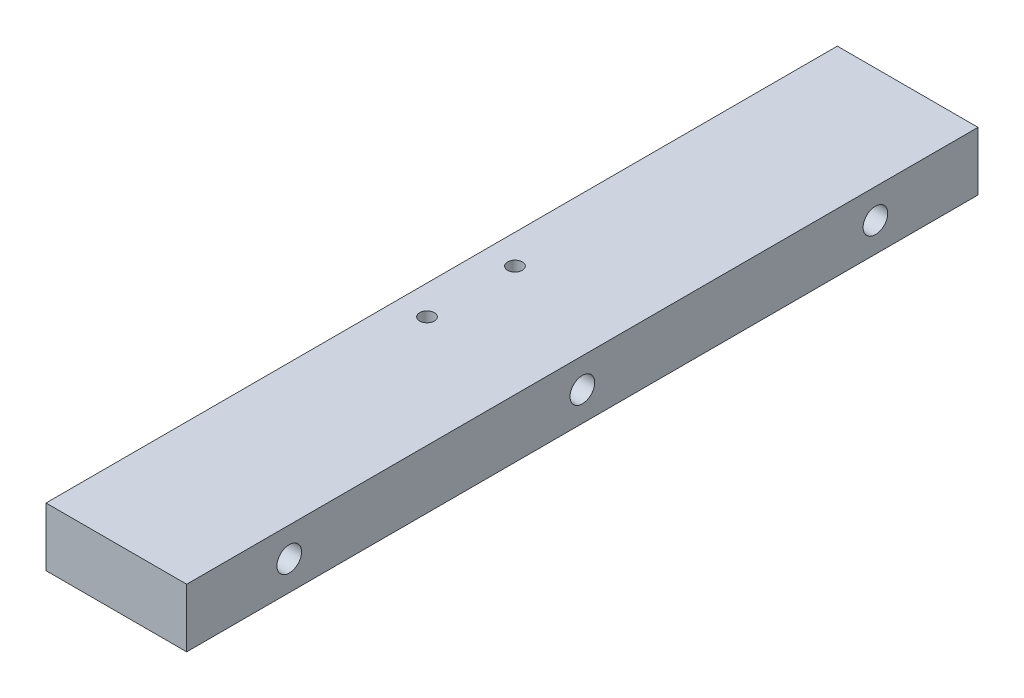
SolidWorks part; units mm, degrees
ref_plane "Front" through (0, 0, 0) normal (0, 0, 1) x (1, 0, 0)
ref_plane "Top" through (0, 0, 0) normal (0, 1, 0) x (1, 0, 0)
ref_plane "Right" through (0, 0, 0) normal (1, 0, 0) x (0, 0, -1)
sketch "Sketch1" plane through (0, 0, 0) normal (0, 1, 0) x (1, 0, 0)
  line L0 (-17.0145, 0) -> (36.7908, 0) construction
  line L1 (0, -67.5) -> (24, -67.5)
  line L2 (0, -67.5) -> (0, 67.5)
  line L3 (0, 67.5) -> (24, 67.5)
  line L4 (24, -67.5) -> (24, 67.5)
  dimension "D1" = 135
  dimension "D2" = 24
extrude "Boss-Extrude1" add sketch "Sketch1" along normal blind 10
hole_wizard "M5x0.8 Tapped Hole1" positions "Sketch3" profile "Sketch2" tap size "M5x0.8" standard "JIS"
sketch "Sketch3" plane through (24, 0, 0) normal (1, 0, 0) x (0, 0, -1)
  line L0 (0, 19.7084) -> (0, -9.2288) construction
  line L2 (-67.5, 0) -> (67.5, 0) construction
  point P0 (0, 5)
  point P1 (-50, 5)
  point P3 (50, 5)
  dimension "D1" = 100
  dimension "D2" = 5
sketch "Sketch2" plane through (24, 5, 0) normal (0, 1, 0) x (0, 0, -1)
  line L0 (0, 0) -> (0, 13.6618)
  line L1 (0, 13.6618) -> (2.1, 12.4)
  line L2 (2.1, 12.4) -> (2.1, 0)
  line L5 (2.1, 0) -> (0, 0)
  line L10 (0, 13.6618) -> (-2.1, 12.4) construction
  line L11 (0, -6.35) -> (0, 107.95) construction
  dimension "Tap Drill Dia." = 4.2
  dimension "Tap Drill Depth" = 12.4
  dimension "Drill Angle" = 118
cosmetic thread "Hole Thread1" parameters "D1"=10, "D2"=5
cosmetic thread "Hole Thread2" parameters "D1"=10, "D2"=5
cosmetic thread "Hole Thread3" parameters "D1"=10, "D2"=5
cosmetic thread "Hole Thread5" parameters "D1"=10, "D2"=5
hole_wizard "M5x0.8 Tapped Hole2" positions "Sketch5" profile "Sketch4" tap size "M5x0.8" standard "JIS"
sketch "Sketch5" plane through (0, 0, 0) normal (-1, 0, 0) x (0, 0, 1)
  point P0 (50, 5)
  point P1 (0, 5)
  point P3 (-50, 5)
sketch "Sketch4" plane through (0, 5, 50) normal (0, 1, 0) x (0, 0, 1)
  line L0 (0, 0) -> (0, 13.6618)
  line L1 (0, 13.6618) -> (2.1, 12.4)
  line L2 (2.1, 12.4) -> (2.1, 0)
  line L5 (2.1, 0) -> (0, 0)
  line L10 (0, 13.6618) -> (-2.1, 12.4) construction
  line L11 (0, -6.35) -> (0, 107.95) construction
  dimension "Tap Drill Dia." = 4.2
  dimension "Tap Drill Depth" = 12.4
  dimension "Drill Angle" = 118
cosmetic thread "Hole Thread4" parameters "D1"=10, "D2"=5
cosmetic thread "Hole Thread6" parameters "D1"=10, "D2"=5
hole_wizard "M3x0.5 Tapped Hole1" positions "Sketch7" profile "Sketch6" tap size "M3x0.5" standard "JIS" end condition through all
sketch "Sketch7" plane through (0, 10, 0) normal (0, 1, 0) x (-1, 0, 0)
  line L0 (-32.0031, 0) -> (4.8, 0) construction
  line L2 (0, -67.5) -> (0, 67.5) construction
  point P0 (-5, -7.5)
  point P1 (-5, 7.5)
  dimension "D1" = 15
  dimension "D2" = 5
cosmetic thread "Hole Thread7" parameters "D2"=3
cosmetic thread "Hole Thread8" parameters "D2"=3
sketch "Sketch6" plane through (5, 10, -7.5) normal (1, 0, 0) x (0, 0, 1)
  line L0 (0, 0) -> (0, 10)
  line L1 (0, 10) -> (1.25, 10)
  line L2 (1.25, 10) -> (1.25, 0)
  line L5 (1.25, 0) -> (0, 0)
  line L11 (0, -6.35) -> (0, 107.95) construction
  dimension "Thru Tap Drill Dia." = 2.5
  dimension "Thru Tap Drill Depth" = 10
